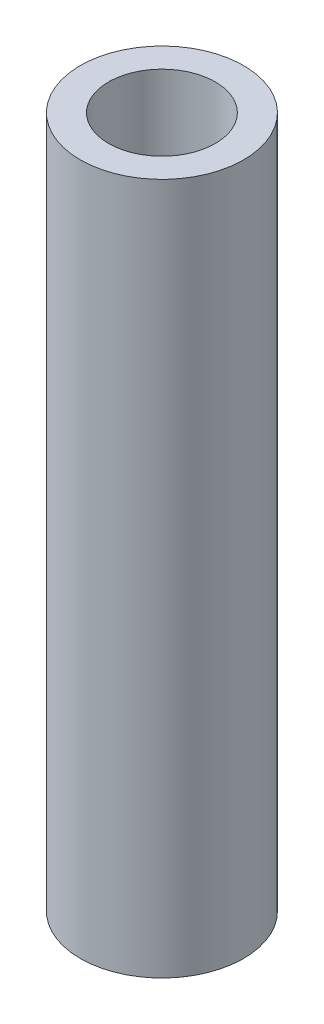
SolidWorks part; units mm, degrees
ref_plane "Front Plane" through (0, 0, 0) normal (0, 0, 1) x (1, 0, 0)
ref_plane "Top Plane" through (0, 0, 0) normal (0, 1, 0) x (1, 0, 0)
ref_plane "Right Plane" through (0, 0, 0) normal (1, 0, 0) x (0, 0, -1)
sketch "Sketch1" plane through (0, 0, 0) normal (0, 1, 0) x (1, 0, 0)
  circle A0 centre (0, 0) radius 2.4892
  circle A1 centre (0, 0) radius 3.81
  dimension "D1" = 4.9784
  dimension "D2" = 7.62
extrude "Boss-Extrude1" add sketch "Sketch1" along normal blind 32.258
